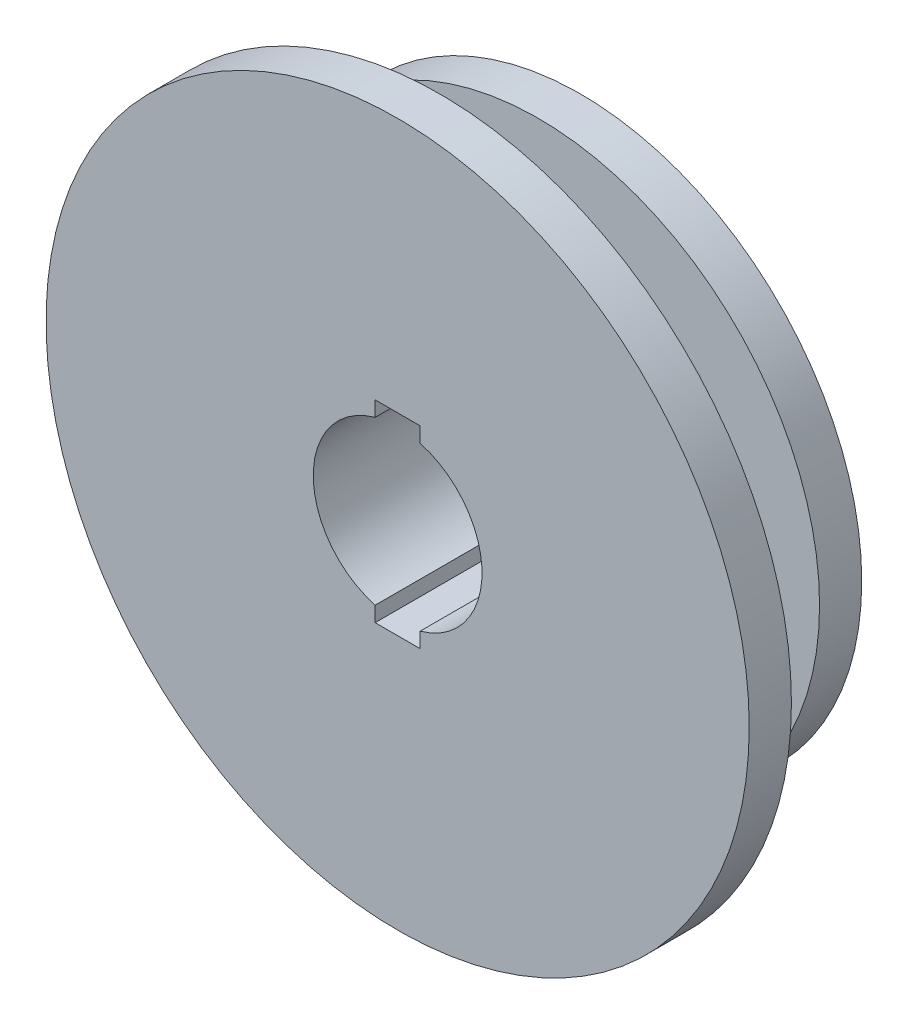
SolidWorks part; units mm, degrees
ref_plane "Front Plane" through (0, 0, 0) normal (0, 0, 1) x (1, 0, 0)
ref_plane "Top Plane" through (0, 0, 0) normal (0, 1, 0) x (1, 0, 0)
ref_plane "Right Plane" through (0, 0, 0) normal (1, 0, 0) x (0, 0, -1)
sketch "Sketch2" plane through (0, 0, 0) normal (1, 0, 0) x (0, 0, -1)
  line L0 (0, 5.8245) -> (79.0958, 5.8245) construction
  line L2 (-31.9421, 65.8245) -> (-31.9421, 255.8245)
  line L3 (-31.9421, 255.8245) -> (-1.9421, 255.8245)
  line L4 (-1.9421, 255.8245) -> (-1.9421, 95.8245)
  line L5 (-1.9421, 95.8245) -> (68.0579, 95.8245)
  line L6 (68.0579, 95.8245) -> (68.0579, 205.8245)
  line L7 (68.0579, 205.8245) -> (98.0579, 205.8245)
  line L10 (98.0579, 205.8245) -> (98.0579, 35.8245)
  line L11 (-31.9421, 65.8245) -> (68.0579, 65.8245)
  line L12 (68.0579, 65.8245) -> (68.0579, 35.8245)
  line L13 (68.0579, 35.8245) -> (98.0579, 35.8245)
  point P2 (0, 0)
  point P12 (98.0579, 203.2349)
  point P14 (87.1583, 65.8245)
  dimension "D1" = 100
  dimension "D2" = 250
  dimension "D3" = 60
  dimension "D4" = 30
  dimension "D5" = 30
  dimension "D7" = 30
  dimension "D8" = 200
  dimension "D10" = 30
revolve "Revolve1" add sketch "Sketch2" angle 360 about L0
sketch "Sketch3" plane through (0, 0, 31.9421) normal (0, 0, 1) x (1, 0, 0)
  line L0 (0, 0) -> (0, 74.4377) construction
  line L1 (16, 74.4377) -> (-16, 74.4377)
  line L2 (-16, 74.4377) -> (-16, 63.6518)
  line L3 (16, 74.4377) -> (16, 63.6518)
  circle A2 centre (0, 5.8245) radius 60 construction
  circle A3 centre (0, 5.8245) radius 60
  point P10 (0, 74.4377)
  dimension "D1" = 32
extrude "Cut-Extrude1" cut sketch "Sketch3" against normal up to surface (100 mm away)
pattern_circular "CirPattern1" count 2 over 360 about axis through (0, 5.8245, 0) along (0, 0, 1) of "Cut-Extrude1"
